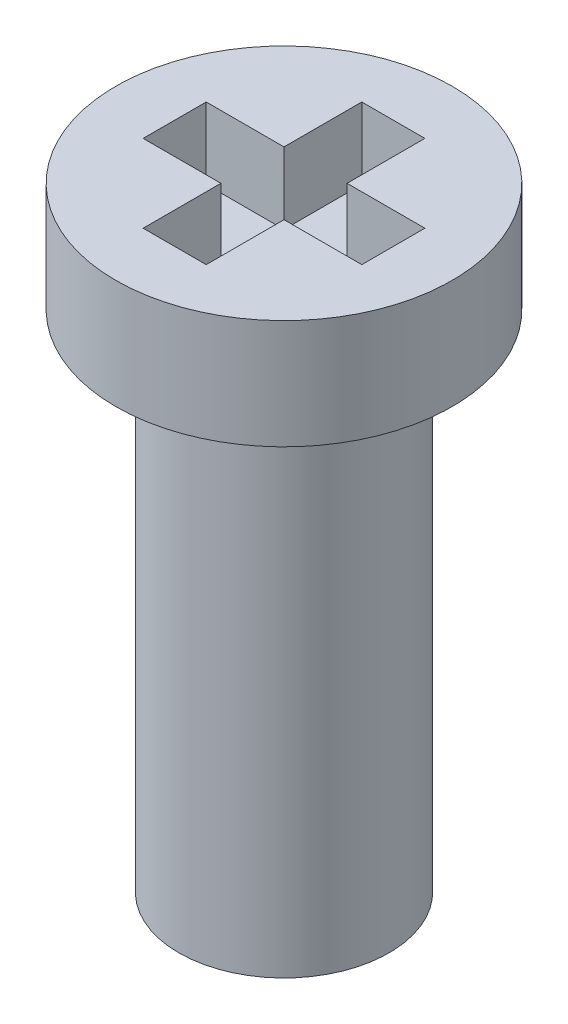
SolidWorks part; units mm, degrees
ref_plane "Front Plane" through (0, 0, 0) normal (0, 0, 1) x (1, 0, 0)
ref_plane "Top Plane" through (0, 0, 0) normal (0, 1, 0) x (1, 0, 0)
ref_plane "Right Plane" through (0, 0, 0) normal (1, 0, 0) x (0, 0, -1)
sketch "Sketch1" plane through (0, 0, 0) normal (1, 0, 0) x (0, 0, -1)
  line L0 (0, 0) -> (0, 7.3) construction
  line L1 (0, 7.3) -> (2, 7.3)
  line L2 (2, 7.3) -> (2, 6)
  line L3 (2, 6) -> (1.25, 6)
  line L4 (1.25, 6) -> (1.25, 0)
  line L5 (1.25, 0) -> (0, 0)
  line L6 (0, 0) -> (0, 7.3)
  dimension "D1" = 7.3
  dimension "D2" = 4
  dimension "D3" = 1.3
  dimension "D4" = 2.5
revolve "Revolve1" add sketch "Sketch1" angle 360 about L0
thread "Thread1" pitch 0.7 start angle 0, offset 0, length 10, pitch 0.7, diameter 2.5
ref_plane "Plane1" through (-1.25, 6, 0) normal (0, 0, 1) x (-1, 0, 0)
sketch "Thread Profile1" plane through (-1.25, 6, 0) normal (0, 0, 1) x (-1, 0, 0)
  line L0 (0, 0) -> (0, 0.7) construction
  line L11 (0, 0) -> (0, 0.6125)
  line L12 (0, 0.6125) -> (-0.3789, 0.3937)
  line L13 (-0.3789, 0.3937) -> (-0.3789, 0.2187)
  line L15 (-0.3789, 0.2187) -> (0, 0)
  line L17 (-0.3789, 0.3062) -> (0, 0.3062) construction
  point P2 (0, 0)
  dimension "Pitch" = 0.7
  dimension "Profile_Angle" = 60
  dimension "Profile_Land" = 0.175
  dimension "Profile_Height" = 0.3789
sketch "Sketch4" plane through (0, 7.3, 0) normal (0, 1, 0) x (1, 0, 0)
  line L0 (0.375, -0.375) -> (0.375, -1.3)
  line L1 (0.375, 0.375) -> (-0.375, -0.375) construction
  line L2 (-0.375, 1.3) -> (-0.375, 0.375)
  line L3 (1.3, 0.375) -> (0.375, 0.375)
  line L4 (0.375, 1.3) -> (0.375, 0.375)
  line L5 (1.3, -0.375) -> (0.375, -0.375)
  line L6 (0.375, -1.3) -> (-0.375, -1.3)
  line L7 (-1.3, -0.375) -> (-1.3, 0.375)
  line L8 (1.3, -0.375) -> (1.3, 0.375)
  line L9 (0.375, 1.3) -> (-0.375, 1.3)
  line L10 (-0.375, 0.375) -> (0.375, -0.375) construction
  line L11 (-0.375, -0.375) -> (-1.3, -0.375)
  line L12 (1.3, 0) -> (-1.3, 0) construction
  line L13 (0, -1.3) -> (0, 1.3) construction
  line L14 (-0.375, -0.375) -> (-0.375, -1.3)
  line L16 (-0.375, 0.375) -> (-1.3, 0.375)
  point P2 (0, 0)
  point P4 (0, 0)
  point P5 (0, 0)
  point P7 (0, 0)
  point P22 (0, 0)
  dimension "D3" = 2.6
  dimension "D1" = 2.6
  dimension "D2" = 0.75
extrude "Cut-Extrude1" cut sketch "Sketch4" against normal blind 0.85
